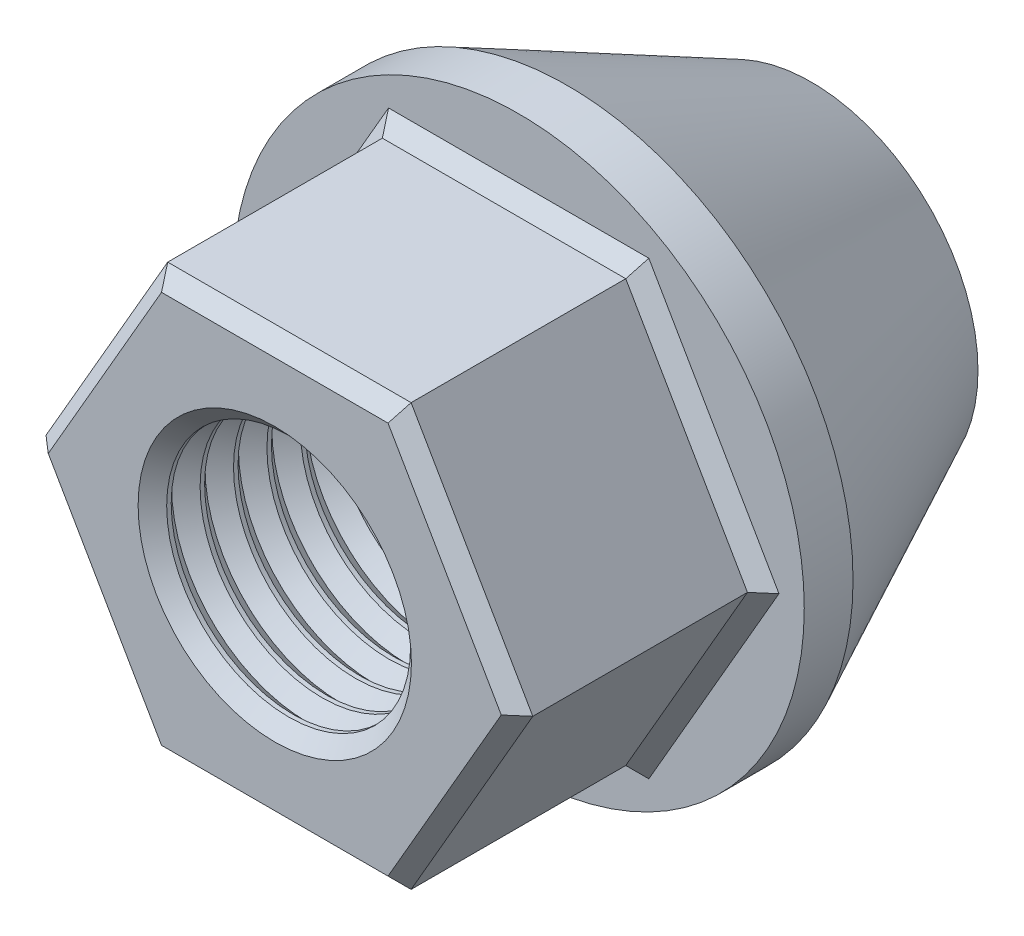
SolidWorks part; units mm, degrees
ref_plane "Front Plane" through (0, 0, 0) normal (0, 0, 1) x (1, 0, 0)
ref_plane "Top Plane" through (0, 0, 0) normal (0, 1, 0) x (1, 0, 0)
ref_plane "Right Plane" through (0, 0, 0) normal (1, 0, 0) x (0, 0, -1)
sketch "Sketch2" plane through (0, 0, 0) normal (0, 0, 1) x (1, 0, 0)
  line L1 (12.6734, 0) -> (6.3367, 10.9755)
  line L2 (6.3367, 10.9755) -> (-6.3367, 10.9755)
  line L3 (-6.3367, 10.9755) -> (-12.6734, 0)
  line L4 (-12.6734, 0) -> (-6.3367, -10.9755)
  line L5 (-6.3367, -10.9755) -> (6.3367, -10.9755)
  line L6 (6.3367, -10.9755) -> (12.6734, 0)
  circle A0 centre (0, 0) radius 10.9755 construction
extrude "Extrude1" add sketch "Sketch2" along normal blind 12.7
sketch "Sketch3" plane through (0, 0, 0) normal (0, 0, -1) x (-1, 0, 0)
  circle A0 centre (0, 0) radius 14.8695
extrude "Extrude2" add sketch "Sketch3" along normal blind 2.54
chamfer "Chamfer1" distance 0.762 angle 45 6 edges at (0, 10.9755, 0) (-9.505, 5.4877, 0) (-9.505, -5.4877, 0) (0, -10.9755, 0) (9.505, -5.4877, 0) (9.505, 5.4877, 0)
chamfer "Chamfer2" distance 0.762 angle 45 6 edges at (0, -10.9755, 12.7) (-9.505, -5.4877, 12.7) (-9.505, 5.4877, 12.7) (0, 10.9755, 12.7) (9.505, 5.4877, 12.7) (9.505, -5.4877, 12.7)
sketch "Sketch5" plane through (0, 0, -2.54) normal (0, 0, -1) x (-1, 0, 0)
  circle A0 centre (0, 0) radius 14.8695
extrude "Extrude3" add sketch "Sketch5" along normal blind 12.7 draft 26
sketch "Sketch4" plane through (0, 0, 12.7) normal (0, 0, 1) x (1, 0, 0)
  circle A0 centre (0, 0) radius 6.35
  dimension "D1" = 12.7
extrude "Cut-Extrude1" cut sketch "Sketch4" against normal through all
ref_plane "Plane1" through (0, 0, 15.24) normal (0, 0, 1) x (1, 0, 0)
sketch "Sketch6" plane through (0, 0, 15.24) normal (0, 0, 1) x (1, 0, 0)
  circle A0 centre (0, 0) radius 5.715
  dimension "D1" = 11.43
sketch "Sketch7" plane through (0, 0, 0) normal (0, 1, 0) x (1, 0, 0)
  line L0 (6.3404, -11.9694) -> (7.1155, -12.7)
  line L2 (7.1155, -12.7) -> (6.3404, -13.4934)
  line L3 (6.3404, -13.4934) -> (5.5915, -12.7)
  line L4 (5.5915, -12.7) -> (6.3404, -11.9694)
  dimension "D1" = 1.524
  dimension "D2" = 1.524
revolve "Cut-Revolve1" cut sketch "Sketch7" angle 360 about axis through (0, 0, -15.24) along (0, 0, 1)
pattern_linear "LPattern2" count 17 spacing 1.74 along (0, 0, -1) of "Cut-Revolve1"
